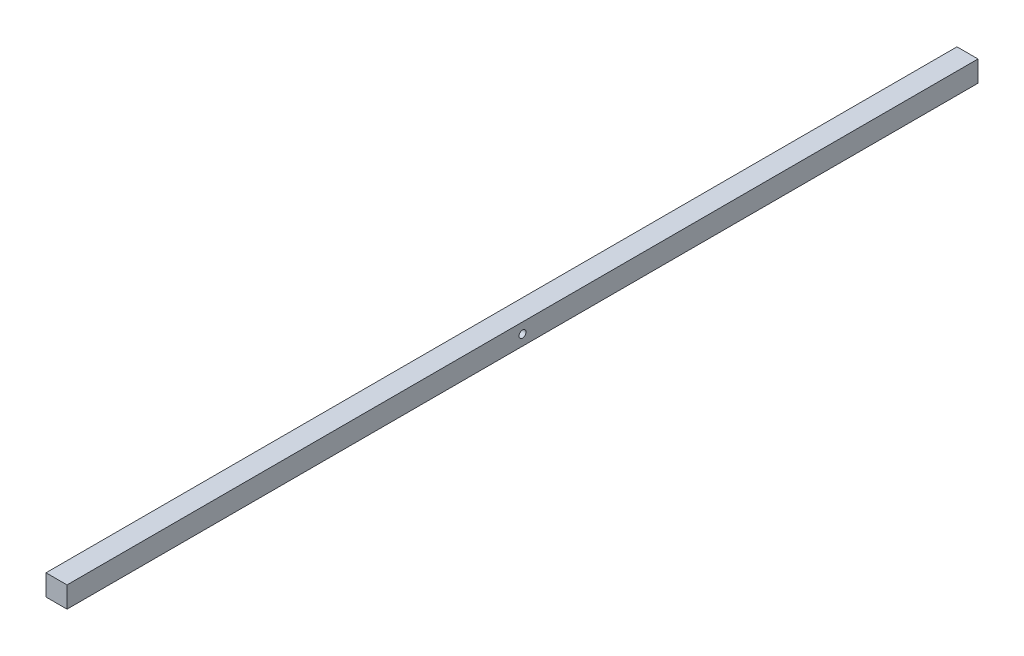
SolidWorks part; units mm, degrees
material "Liga 1060"
ref_plane "Plano frontal" through (0, 0, 0) normal (0, 0, 1) x (1, 0, 0)
ref_plane "Plano superior" through (0, 0, 0) normal (0, 1, 0) x (1, 0, 0)
ref_plane "Plano direito" through (0, 0, 0) normal (1, 0, 0) x (0, 0, -1)
sketch "Esboço1" plane through (0, 0, 0) normal (0, 0, 1) x (1, 0, 0)
  line L1 (-3, -3) -> (3, -3)
  line L2 (-3, -3) -> (-3, 3)
  line L3 (-3, 3) -> (3, 3)
  line L4 (3, -3) -> (3, 3)
  line L5 (-3, -3) -> (3, 3) construction
  line L6 (-3, 3) -> (3, -3) construction
  point P0 (0, 0)
  dimension "D1" = 6
extrude "Ressalto-extrusão1" add sketch "Esboço1" along normal blind 260
sketch "Esboço2" plane through (-3, 0, 0) normal (-1, 0, 0) x (0, 0, 1)
  line L0 (130, 3) -> (130, -3) construction
  line L1 (260, 3) -> (0, 3) construction
  line L2 (260, -3) -> (0, -3) construction
  circle A0 centre (130, 0) radius 1
extrude "Corte-extrusão1" cut sketch "Esboço2" against normal blind 10
